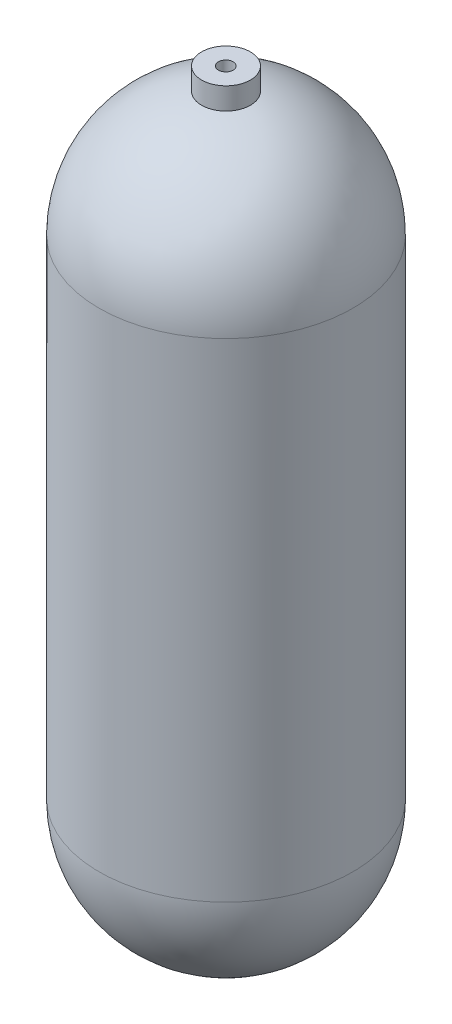
SolidWorks part; units mm, degrees
material "A-Glass Fiber"
ref_plane "Front Plane" through (0, 0, 0) normal (0, 0, 1) x (1, 0, 0)
ref_plane "Top Plane" through (0, 0, 0) normal (0, 1, 0) x (1, 0, 0)
ref_plane "Right Plane" through (0, 0, 0) normal (1, 0, 0) x (0, 0, -1)
sketch "Sketch1" plane through (0, 0, 0) normal (0, 0, 1) x (1, 0, 0)
  line L0 (-277.9989, 0) -> (285.3595, 0) construction
  line L1 (82.55, 400.05) -> (82.55, 82.55)
  line L2 (-223.1734, 482.6) -> (246.1876, 482.6) construction
  line L3 (0, -16.2482) -> (0, 0) construction
  line L4 (79.375, 400.05) -> (79.375, 82.55)
  line L5 (0, 482.6) -> (0, 540.8646) construction
  line L6 (0, 479.425) -> (0, 482.6)
  line L7 (0, 3.175) -> (0, 0)
  arc A0 (0, 0) -> (82.55, 82.55) centre (0, 82.55) ccw
  arc A1 (82.55, 400.05) -> (0, 482.6) centre (0, 400.05) ccw
  arc A2 (79.375, 400.05) -> (0, 479.425) centre (0, 400.05) ccw
  arc A3 (0, 3.175) -> (79.375, 82.55) centre (0, 82.55) ccw
  dimension "D1" = 482.6
  dimension "D2" = 82.55
  dimension "D3" = 3.175
revolve "Revolve1" add sketch "Sketch1" angle 360 about L5
ref_plane "Plane1" through (0, 482.6, 0) normal (0, 1, 0) x (1, 0, 0)
sketch "Sketch2" plane through (0, 482.6, 0) normal (0, 1, 0) x (1, 0, 0)
  circle A0 centre (0, 0) radius 15.875
  dimension "D1" = 31.75
extrude "Boss-Extrude1" add sketch "Sketch2" along normal blind 12.7 and the other way up to next (12.7 mm away) contours A0
sketch "Sketch3" plane through (0, 495.3, 0) normal (0, 1, 0) x (1, 0, 0)
  line L0 (0, 28.2988) -> (0, -59.228) construction
  line L1 (-76.1012, 0) -> (75.6366, 0) construction
hole_wizard "3/8 (0.375) Diameter Hole1" positions "3DSketch1" profile "Sketch5" hole size "3/8" standard "ANSI Inch"
sketch3d "3DSketch1"
  point P0 (-0.0532, 495.3, 0.0938)
  point P3 (0, 0, 0)
sketch "Sketch5" plane through (-0.0532, 495.3, 0.0938) normal (1, 0, 0) x (0, 0, 1)
  line L0 (0, 0) -> (0, 28.2616)
  line L1 (0, 28.2616) -> (4.7625, 25.4)
  line L2 (4.7625, 25.4) -> (4.7625, 0)
  line L5 (4.7625, 0) -> (0, 0)
  line L10 (0, 28.2616) -> (-4.7625, 25.4) construction
  line L11 (0, -6.35) -> (0, 107.95) construction
  dimension "Hole Dia." = 9.525
  dimension "Hole Depth" = 25.4
  dimension "Drill Angle" = 118
